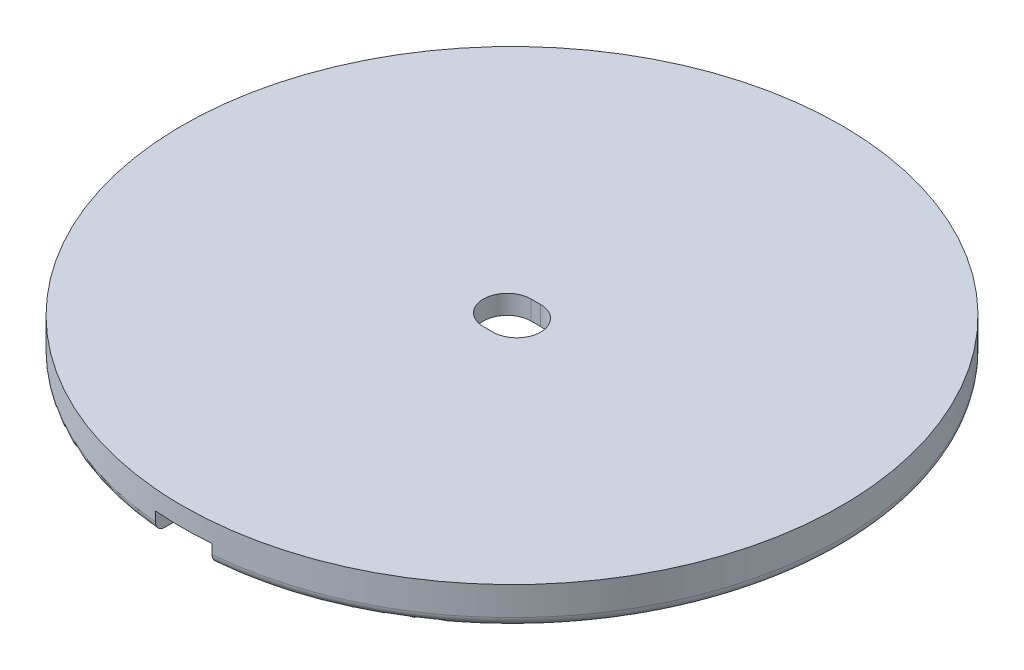
SolidWorks part; units mm, degrees
ref_plane "Front Plane" through (0, 0, 0) normal (0, 0, 1) x (1, 0, 0)
ref_plane "Top Plane" through (0, 0, 0) normal (0, 1, 0) x (1, 0, 0)
ref_plane "Right Plane" through (0, 0, 0) normal (1, 0, 0) x (0, 0, -1)
sketch "Sketch1" plane through (0, 0, 0) normal (0, 1, 0) x (1, 0, 0)
  circle A0 centre (0, 0) radius 34.5
  dimension "D1" = 69
extrude "Boss-Extrude1" add sketch "Sketch1" along normal blind 4
sketch "Sketch2" plane through (0, 4, 0) normal (0, 1, 0) x (1, 0, 0)
  line L0 (0.5, 0) -> (-0.5, 0) construction
  line L1 (0.5, -2.5) -> (-0.5, -2.5)
  line L2 (0.5, 2.5) -> (-0.5, 2.5)
  arc A0 (0.5, -2.5) -> (0.5, 2.5) centre (0.5, 0) ccw
  arc A1 (-0.5, 2.5) -> (-0.5, -2.5) centre (-0.5, 0) ccw
  point P2 (0, 0)
  point P7 (3, 0)
  point P8 (-3, 0)
  dimension "D1" = 6
  dimension "D2" = 5
  dimension "D3" = 0
  dimension "D4" = 0
extrude "Cut-Extrude1" cut sketch "Sketch2" against normal blind 4
sketch "Sketch3" plane through (0, 0, 0) normal (0, -1, 0) x (1, 0, 0)
  circle A0 centre (0, 0) radius 32.5
  circle A1 centre (0, 0) radius 7.5
  circle A2 centre (0, 0) radius 12.5
  line M2 (-0.5, 2.5) -> (0.5, 2.5)
  arc M3 (0.5, 2.5) -> (0.5, -2.5) centre (0.5, 0) cw
  line M4 (0.5, -2.5) -> (-0.5, -2.5)
  arc M5 (-0.5, -2.5) -> (-0.5, 2.5) centre (-0.5, 0) cw
  dimension "D1" = 65
  dimension "D2" = 15
  dimension "D3" = 5
extrude "Cut-Extrude2" cut sketch "Sketch3" against normal blind 2 contours A0 A2 | A1 M5 M2 M3 M4
sketch "Sketch4" plane through (0, 0, 0) normal (0, -1, 0) x (1, 0, 0)
  line L1 (2.9658, 6.8887) -> (-2.9658, 6.8887)
  line L2 (2.9658, 6.8887) -> (2.9658, 37.0461)
  line L3 (2.9658, 37.0461) -> (-2.9658, 37.0461)
  line L4 (-2.9658, 6.8887) -> (-2.9658, 37.0461)
  circle A0 centre (0, 0) radius 7.5 construction
  point P6 (0, 6.8887)
  dimension "D1" = 0
extrude "Cut-Extrude3" cut sketch "Sketch4" against normal blind 2
fillet "Fillet1" radius 1 1 edges at (0, 0, -34.5)
